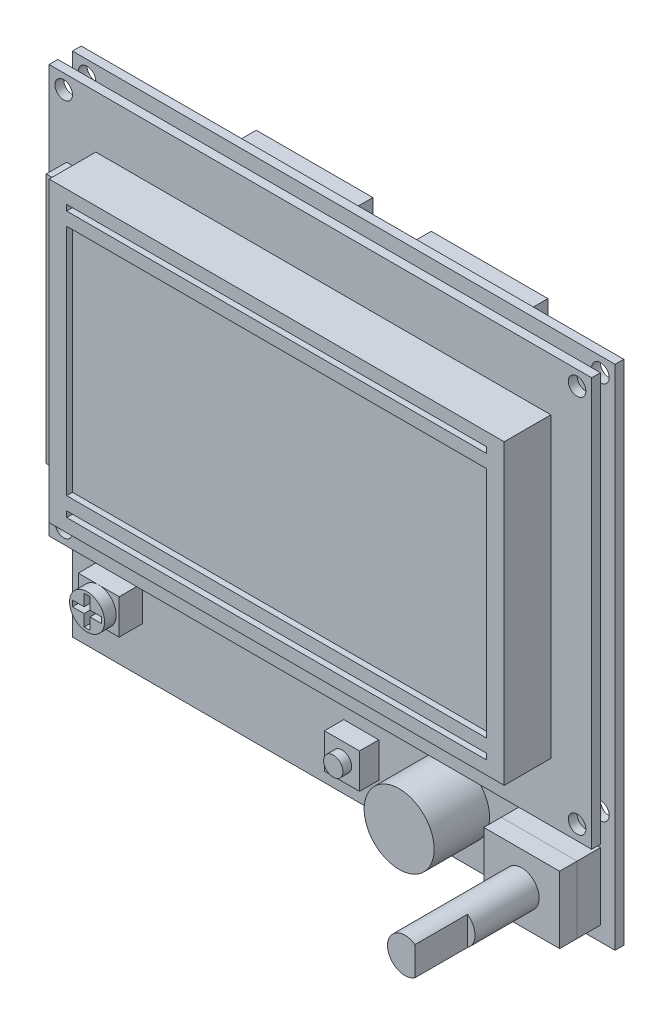
SolidWorks part; units mm, degrees
material "7075-T6 (SN)"
ref_plane "Plan de face" through (0, 0, 0) normal (0, 0, 1) x (1, 0, 0)
ref_plane "Plan de dessus" through (0, 0, 0) normal (0, 1, 0) x (1, 0, 0)
ref_plane "Plan de droite" through (0, 0, 0) normal (1, 0, 0) x (0, 0, -1)
sketch "Esquisse1" plane through (0, 0, 0) normal (0, 0, 1) x (1, 0, 0)
  line L1 (-39, 0) -> (39, 0)
  line L2 (-39, 0) -> (-39, 51)
  line L3 (-39, 51) -> (39, 51)
  line L4 (39, 0) -> (39, 51)
  dimension "D1" = 78
  dimension "D2" = 51
extrude "Boss.-Extru.1" add sketch "Esquisse1" along normal blind 8
sketch "Esquisse2" plane through (0, 0, 8) normal (0, 0, 1) x (1, 0, 0)
  line L0 (39, 51) -> (-39, 51) construction
  line L1 (-36, 45.5) -> (36, 45.5)
  line L2 (-36, 45.5) -> (-36, 5.5)
  line L3 (-36, 5.5) -> (36, 5.5)
  line L4 (36, 45.5) -> (36, 5.5)
  line L5 (36, 3.25) -> (-36, 3.25)
  line L6 (36, 3.25) -> (36, 2.25)
  line L7 (36, 2.25) -> (-36, 2.25)
  line L8 (-36, 3.25) -> (-36, 2.25)
  line L9 (-36, 47.75) -> (36, 47.75)
  line L10 (-36, 47.75) -> (-36, 48.75)
  line L11 (-36, 48.75) -> (36, 48.75)
  line L12 (36, 47.75) -> (36, 48.75)
  line L13 (0, 51) -> (0, 0) construction
  line L14 (-39, 25.5) -> (39, 25.5) construction
  line L15 (-39, 51) -> (-39, 0) construction
  line L16 (39, 0) -> (39, 51) construction
  dimension "D1" = 40
  dimension "D2" = 1
  dimension "D3" = 2.25
  dimension "D4" = 51
  dimension "D5" = 72
  dimension "D6" = 78
  dimension "D7" = 3
  dimension "D8" = 2.25
  dimension "D9" = 2.25
extrude "Enlèv. mat.-Extru.1" cut sketch "Esquisse2" against normal blind 1
sketch "Esquisse3" plane through (0, 0, 0) normal (0, 0, -1) x (-1, 0, 0)
  line L0 (39, 25.5) -> (44, 25.5) construction
  line L1 (39, 51) -> (39, 0) construction
  line L3 (39, 47) -> (44, 47)
  line L4 (39, 47) -> (39, 4)
  line L5 (39, 4) -> (44, 4)
  line L6 (44, 47) -> (44, 4)
  dimension "D1" = 43
  dimension "D2" = 5
extrude "Boss.-Extru.2" add sketch "Esquisse3" against normal blind 3.5 separate body
sketch "Esquisse4" plane through (0, 0, 0) normal (0, 0, -1) x (-1, 0, 0)
  line L0 (-46, 25) -> (0.5, 25) construction
  line L1 (-46, 60) -> (47, 60)
  line L2 (-46, 60) -> (-46, -10)
  line L3 (-46, -10) -> (47, -10)
  line L4 (47, 60) -> (47, -10)
  line L5 (0.5, 25) -> (0.5, -10) construction
  line L6 (-39, 51) -> (39, 51) construction
  line L7 (-39, 0) -> (-39, 51) construction
  circle A0 centre (-43.5, 57.5) radius 1.5
  circle A1 centre (-43.5, -7.5) radius 1.5
  circle A2 centre (44.5, 57.5) radius 1.5
  circle A3 centre (44.5, -7.5) radius 1.5
  dimension "D3" = 3
  dimension "D1" = 93
  dimension "D2" = 70
  dimension "D4" = 2.5
  dimension "D5" = 2.5
  dimension "D6" = 9
  dimension "D7" = 7
extrude "Boss.-Extru.3" add sketch "Esquisse4" along normal blind 1.5 separate body
ref_plane "Plan1" through (0, 0, -4) normal (0, 0, -1) x (-1, 0, 0)
sketch "Esquisse5" plane through (0, 0, -4) normal (0, 0, -1) x (-1, 0, 0)
  line L1 (-46, 60) -> (47, 60)
  line L2 (-46, 60) -> (-46, -27)
  line L3 (-46, -27) -> (47, -27)
  line L4 (47, 60) -> (47, -27)
  circle A0 centre (-43.5, 57.5) radius 1.5
  circle A1 centre (-43.5, -7.5) radius 1.5
  circle A2 centre (44.5, -7.5) radius 1.5
  circle A3 centre (44.5, 57.5) radius 1.5
  dimension "D1" = 87
extrude "Boss.-Extru.4" add sketch "Esquisse5" along normal blind 1.5 separate body
sketch "Esquisse6" plane through (-47, 0, 0) normal (-1, 0, 0) x (0, 0, 1)
  line L0 (-5.5, 38.5) -> (-8.5, 38.5)
  line L1 (-5.5, -27) -> (-5.5, 60) construction
  line L2 (-8.5, 38.5) -> (-8.5, 12)
  line L3 (-8.5, 12) -> (-5.5, 12)
  line L4 (-5.5, 60) -> (-4, 60) construction
  line L5 (-5.5, 38.25) -> (-8.25, 38.25)
  line L6 (-8.25, 38.25) -> (-8.25, 12.25)
  line L7 (-8.25, 12.25) -> (-5.5, 12.25)
  line L8 (-5.5, 38.5) -> (-5.5, 38.25)
  line L9 (-5.5, 12.25) -> (-5.5, 12)
  dimension "D1" = 21.5
  dimension "D2" = 26.5
  dimension "D3" = 3
  dimension "D4" = 0.25
extrude "Boss.-Extru.5" add sketch "Esquisse6" against normal blind 25 separate body
sketch "Esquisse7" plane through (0, 0, -5.5) normal (0, 0, -1) x (-1, 0, 0)
  line L0 (47, -27) -> (47, 60) construction
  line L1 (26, 53.5) -> (6, 53.5)
  line L2 (26, 53.5) -> (26, 44.5)
  line L3 (26, 44.5) -> (6, 44.5)
  line L4 (6, 53.5) -> (6, 44.5)
  line L5 (-24, 53.5) -> (-4, 53.5)
  line L6 (-24, 53.5) -> (-24, 44.5)
  line L7 (-24, 44.5) -> (-4, 44.5)
  line L8 (-4, 53.5) -> (-4, 44.5)
  line L9 (47, 60) -> (-46, 60) construction
  line L10 (-23, 52.5) -> (-5, 52.5)
  line L11 (-5, 52.5) -> (-5, 45.5)
  line L12 (-23, 45.5) -> (-5, 45.5)
  line L13 (-23, 52.5) -> (-23, 45.5)
  line L14 (25, 52.5) -> (7, 52.5)
  line L15 (7, 52.5) -> (7, 45.5)
  line L16 (25, 45.5) -> (7, 45.5)
  line L17 (25, 52.5) -> (25, 45.5)
  dimension "D1" = 20
  dimension "D2" = 9
  dimension "D3" = 10
  dimension "D4" = 21
  dimension "D5" = 6.5
  dimension "D6" = 1
extrude "Boss.-Extru.6" add sketch "Esquisse7" along normal blind 9 separate body
sketch "Esquisse8" plane through (0, 0, -4) normal (0, 0, 1) x (1, 0, 0)
  line L0 (46, -27) -> (-47, -27) construction
  line L1 (30.5, -13) -> (43.5, -13)
  line L2 (30.5, -13) -> (30.5, -24.5)
  line L3 (30.5, -24.5) -> (43.5, -24.5)
  line L4 (43.5, -13) -> (43.5, -24.5)
  line L5 (46, 60) -> (46, -27) construction
  line L6 (-47, -27) -> (-47, 60) construction
  line L7 (-42, -13) -> (-35, -13)
  line L8 (-42, -13) -> (-42, -19)
  line L9 (-42, -19) -> (-35, -19)
  line L10 (-35, -13) -> (-35, -19)
  dimension "D1" = 11.5
  dimension "D2" = 13
  dimension "D3" = 2.5
  dimension "D4" = 2.5
  dimension "D5" = 6
  dimension "D6" = 7
  dimension "D7" = 8
  dimension "D8" = 5
extrude "Boss.-Extru.7" add sketch "Esquisse8" along normal blind 4 separate body
sketch "Esquisse9" plane through (0, 0, 0) normal (0, 0, 1) x (1, 0, 0)
  line L0 (30.5, -24.5) -> (43.5, -24.5) construction
  line L1 (43.5, -13) -> (30.5, -13)
  line L2 (43.5, -13) -> (43.5, -24.5)
  line L3 (43.5, -24.5) -> (30.5, -24.5)
  line L4 (30.5, -13) -> (30.5, -24.5)
  line L5 (30.5, -13) -> (30.5, -24.5) construction
extrude "Boss.-Extru.8" add sketch "Esquisse9" along normal blind 3 separate body
sketch "Esquisse10" plane through (0, 0, 3) normal (0, 0, 1) x (1, 0, 0)
  circle A0 centre (37, -18.75) radius 3
  dimension "D1" = 6
extrude "Boss.-Extru.9" add sketch "Esquisse10" along normal blind 20 separate body
sketch "Esquisse11" plane through (0, 0, 23) normal (0, 0, 1) x (1, 0, 0)
  line L1 (38.7143, -16.288) -> (58.9108, -16.288)
  line L2 (38.7143, -16.288) -> (38.7143, -21.212)
  line L3 (38.7143, -21.212) -> (58.9108, -21.212)
  line L4 (58.9108, -16.288) -> (58.9108, -21.212)
  circle A0 centre (37, -18.75) radius 3 construction
extrude "Enlèv. mat.-Extru.2" cut sketch "Esquisse11" against normal blind 9
sketch "Esquisse12" plane through (0, 0, -4) normal (0, 0, 1) x (1, 0, 0)
  line L0 (46, -27) -> (-47, -27) construction
  line L1 (30.5, -13) -> (30.5, -24.5) construction
  circle A0 centre (18.5, -18) radius 6
  dimension "D1" = 12
  dimension "D2" = 9
  dimension "D3" = 12
extrude "Boss.-Extru.10" add sketch "Esquisse12" along normal blind 9.5 separate body
sketch "Esquisse13" plane through (0, 0, 0) normal (0, 0, 1) x (1, 0, 0)
  line L0 (-38, -13.5) -> (-39, -13.5)
  line L1 (-39, -13.5) -> (-39, -15.5)
  line L2 (-39, -15.5) -> (-41, -15.5)
  line L3 (-41, -15.5) -> (-41, -16.5)
  line L4 (-41, -16.5) -> (-39, -16.5)
  line L5 (-39, -16.5) -> (-39, -18.5)
  line L6 (-39, -18.5) -> (-38, -18.5)
  line L7 (-38, -18.5) -> (-38, -16.5)
  line L8 (-38, -16.5) -> (-36, -16.5)
  line L9 (-36, -16.5) -> (-36, -15.5)
  line L10 (-36, -15.5) -> (-38, -15.5)
  line L11 (-38, -15.5) -> (-38, -13.5)
  line L12 (-35, -19) -> (-42, -13) construction
  line L13 (-42, -13) -> (-42, -19) construction
  circle A0 centre (-38.5, -16) radius 3
  dimension "D1" = 1
  dimension "D2" = 2
  dimension "D3" = 0.5
  dimension "D4" = 0.5
extrude "Boss.-Extru.11" add sketch "Esquisse13" along normal blind 2 separate body
sketch "Esquisse14" plane through (0, 0, -4) normal (0, 0, 1) x (1, 0, 0)
  line L0 (46, -27) -> (-47, -27) construction
  line L1 (-0.5, -16) -> (5.5, -16)
  line L2 (-0.5, -16) -> (-0.5, -22)
  line L3 (-0.5, -22) -> (5.5, -22)
  line L4 (5.5, -16) -> (5.5, -22)
  line L5 (-47, -27) -> (-47, 60) construction
  dimension "D1" = 6
  dimension "D2" = 6
  dimension "D3" = 5
  dimension "D4" = 46.5
extrude "Boss.-Extru.12" add sketch "Esquisse14" along normal blind 3.3 separate body
sketch "Esquisse15" plane through (0, 0, -0.7) normal (0, 0, 1) x (1, 0, 0)
  line L0 (-0.5, -16) -> (5.5, -22) construction
  circle A0 centre (2.5, -19) radius 1.65
  dimension "D1" = 3.3
extrude "Boss.-Extru.13" add sketch "Esquisse15" along normal blind 1.5 separate body
equation "\"D7@Esquisse2\"=(\"D6@Esquisse2\"-\"D5@Esquisse2\")/2"
equation "\"D8@Esquisse2\"=\"D3@Esquisse2\""
equation "\"D9@Esquisse2\"=\"D3@Esquisse2\""
equation "\"D3@Esquisse2\"=(\"D4@Esquisse2\"-\"D1@Esquisse2\"-(2*\"D2@Esquisse2\"))/4"
